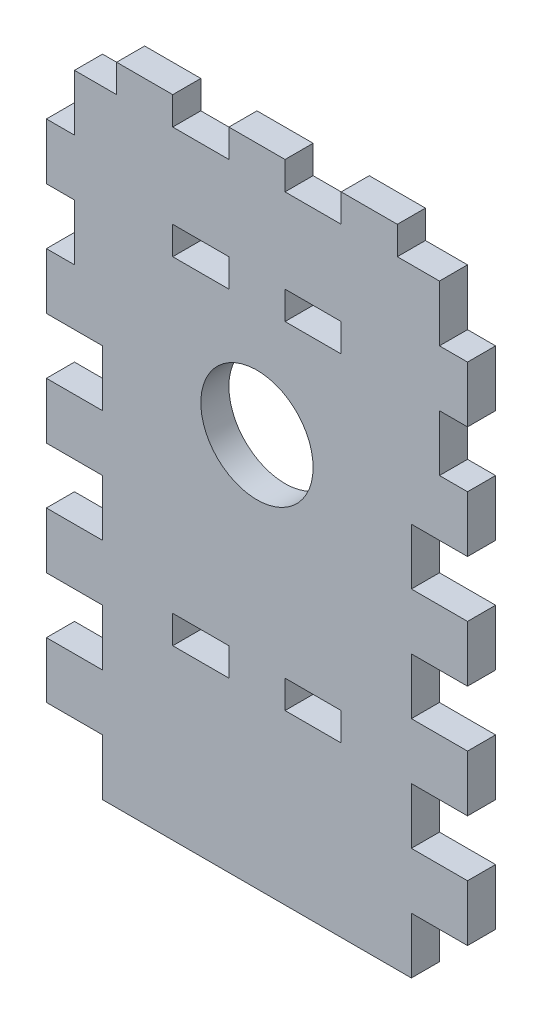
SolidWorks part; units mm, degrees
material "Pine"
ref_plane "Front Plane" through (0, 0, 0) normal (0, 0, 1) x (1, 0, 0)
ref_plane "Top Plane" through (0, 0, 0) normal (0, 1, 0) x (1, 0, 0)
ref_plane "Right Plane" through (0, 0, 0) normal (1, 0, 0) x (0, 0, -1)
sketch "Sketch1" plane through (0, 0, 0) normal (0, 0, 1) x (1, 0, 0)
  line L1 (0, 0) -> (95.25, 0)
  line L2 (0, 0) -> (0, 177.8)
  line L3 (0, 177.8) -> (95.25, 177.8)
  line L4 (95.25, 0) -> (95.25, 177.8)
  dimension "D1" = 95.25
  dimension "D2" = 177.8
extrude "Boss-Extrude1" add sketch "Sketch1" along normal blind 6.35 contours L3 L4 L1 L2
sketch "Sketch2" plane through (0, 0, 6.35) normal (0, 0, 1) x (1, 0, 0)
  line L0 (0, 0) -> (0, 177.8) construction
  line L1 (0, 12.7) -> (12.7, 12.7)
  line L2 (0, 12.7) -> (0, 0)
  line L3 (0, 0) -> (12.7, 0)
  line L4 (12.7, 12.7) -> (12.7, 0)
  line L5 (0, 0) -> (95.25, 0) construction
  line L6 (95.25, 0) -> (95.25, 177.8) construction
  line L7 (95.25, 12.7) -> (82.55, 12.7)
  line L8 (95.25, 12.7) -> (95.25, 0)
  line L9 (95.25, 0) -> (82.55, 0)
  line L10 (82.55, 12.7) -> (82.55, 0)
  dimension "D1" = 12.7
  dimension "D2" = 12.7
extrude "Cut-Extrude1" cut sketch "Sketch2" against normal through all
pattern_linear "LPattern1" count 4 spacing 25.4 along (0, 1, 0) of "Cut-Extrude1"
sketch "Sketch3" plane through (0, 0, 6.35) normal (0, 0, 1) x (1, 0, 0)
  line L0 (47.625, 0) -> (47.625, 41.275) construction
  line L1 (28.575, 44.45) -> (41.275, 44.45)
  line L2 (28.575, 44.45) -> (28.575, 38.1)
  line L3 (28.575, 38.1) -> (41.275, 38.1)
  line L4 (41.275, 44.45) -> (41.275, 38.1)
  line L5 (53.975, 44.45) -> (66.675, 44.45)
  line L6 (53.975, 44.45) -> (53.975, 38.1)
  line L7 (53.975, 38.1) -> (66.675, 38.1)
  line L8 (66.675, 44.45) -> (66.675, 38.1)
  line L9 (12.7, 0) -> (82.55, 0) construction
  line L10 (41.275, 41.275) -> (53.975, 41.275) construction
  dimension "D1" = 12.7
  dimension "D2" = 6.35
  dimension "D3" = 38.1
extrude "Cut-Extrude2" cut sketch "Sketch3" against normal through all
sketch "Sketch4" plane through (0, 0, 6.35) normal (0, 0, 1) x (1, 0, 0)
  line L0 (44.45, 163.25) -> (44.45, 99.25) construction
  line L1 (0, 88.9) -> (0, 177.8) construction
  line L2 (12.7, 0) -> (82.55, 0) construction
  line L4 (44.45, 163.25) -> (57.15, 163.25) construction
  line L5 (44.45, 163.25) -> (44.45, 99.25) construction
  line L6 (44.45, 99.25) -> (57.15, 99.25) construction
  line L7 (57.15, 163.25) -> (57.15, 99.25) construction
  circle A0 centre (44.45, 163.25) radius 1.75
  circle A1 centre (44.45, 99.25) radius 1.75
  circle A2 centre (57.15, 163.25) radius 1.75
  circle A3 centre (57.15, 99.25) radius 1.75
  dimension "D4" = 3.5
  dimension "D1" = 44.45
  dimension "D2" = 64
  dimension "D3" = 99.25
  dimension "D5" = 12.7
sketch "Sketch5" plane through (0, 0, 6.35) normal (0, 0, 1) x (1, 0, 0)
  line L0 (0, 88.9) -> (0, 177.8) construction
  line L1 (0, 101.6) -> (6.35, 101.6)
  line L2 (0, 101.6) -> (0, 114.3)
  line L3 (0, 114.3) -> (6.35, 114.3)
  line L4 (6.35, 101.6) -> (6.35, 114.3)
  line L5 (95.25, 88.9) -> (95.25, 177.8) construction
  line L6 (95.25, 114.3) -> (88.9, 114.3)
  line L7 (95.25, 114.3) -> (95.25, 101.6)
  line L8 (95.25, 101.6) -> (88.9, 101.6)
  line L9 (88.9, 114.3) -> (88.9, 101.6)
  line L10 (12.7, 76.2) -> (12.7, 88.9) construction
  line L11 (12.7, 88.9) -> (0, 88.9) construction
  dimension "D1" = 12.7
  dimension "D2" = 6.35
extrude "Cut-Extrude4" cut sketch "Sketch5" against normal through all
pattern_linear "LPattern2" count 4 spacing 25.4 along (0, 1, 0) of "Cut-Extrude4"
sketch "Sketch6" plane through (0, 0, 6.35) normal (0, 0, 1) x (1, 0, 0)
  line L1 (0, 177.8) -> (95.25, 177.8)
  line L2 (0, 177.8) -> (0, 139.7)
  line L3 (0, 139.7) -> (95.25, 139.7)
  line L4 (95.25, 177.8) -> (95.25, 139.7)
extrude "Cut-Extrude5" cut sketch "Sketch6" against normal through all
sketch "Sketch7" plane through (0, 139.7, 0) normal (0, 1, 0) x (1, 0, 0)
  line L0 (6.35, 0) -> (88.9, 0) construction
  line L1 (41.275, 0) -> (53.975, 0)
  line L2 (41.275, 0) -> (41.275, -6.35)
  line L3 (41.275, -6.35) -> (53.975, -6.35)
  line L4 (53.975, 0) -> (53.975, -6.35)
  line L5 (6.35, -6.35) -> (88.9, -6.35) construction
  point P8 (47.625, -6.35)
  dimension "D1" = 12.7
extrude "Boss-Extrude2" add sketch "Sketch7" along normal blind 6.35
pattern_linear "LPattern3" count 2 spacing 25.4 along (1, 0, 0) count 2 spacing 25.4 along (-1, 0, 0) of "Boss-Extrude2"
pattern_linear "LPattern4" count 2 spacing 76.2 along (0, 1, 0) of "Cut-Extrude2"
sketch "Sketch8" plane through (0, 0, 6.35) normal (0, 0, 1) x (1, 0, 0)
  line L0 (47.625, 146.05) -> (47.625, 88.9) construction
  line L1 (41.275, 146.05) -> (53.975, 146.05) construction
  line L2 (12.7, 88.9) -> (0, 88.9) construction
  circle A0 centre (47.625, 88.9) radius 12.7
  dimension "D1" = 25.4
extrude "Cut-Extrude6" cut sketch "Sketch8" against normal through all
